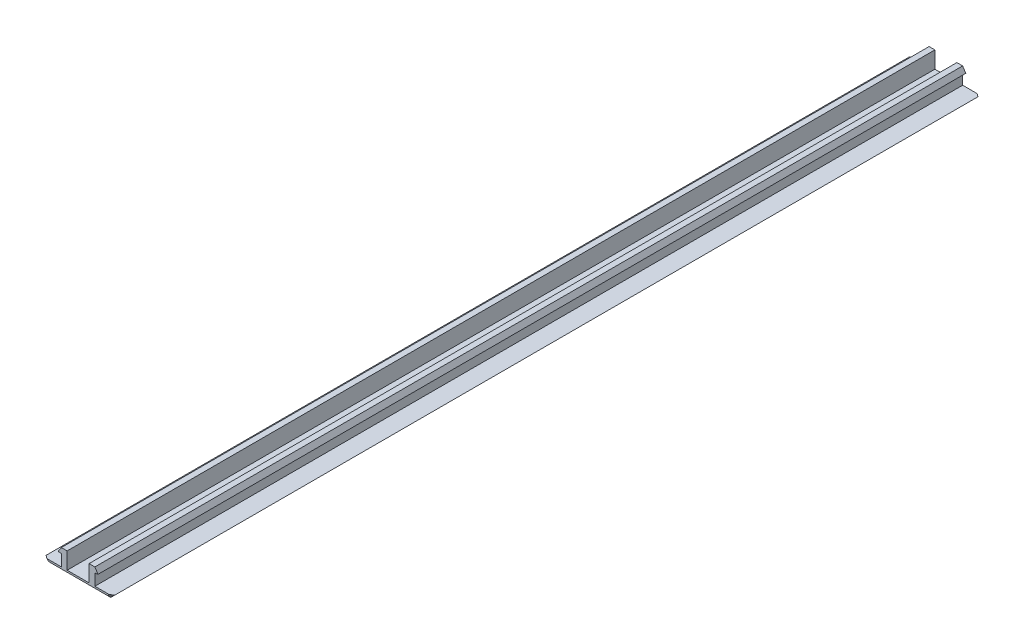
SolidWorks part; units mm, degrees
ref_plane "Front Plane" through (0, 0, 0) normal (0, 0, 1) x (1, 0, 0)
ref_plane "Top Plane" through (0, 0, 0) normal (0, 1, 0) x (1, 0, 0)
ref_plane "Right Plane" through (0, 0, 0) normal (1, 0, 0) x (0, 0, -1)
sketch "Sketch1" plane through (0, 0, 0) normal (0, 0, 1) x (1, 0, 0)
  line L0 (5.95, 0.7071) -> (2.9, 0.7071)
  line L1 (2.9, 0.7071) -> (2.9, 2.6888)
  line L2 (2.9, 2.6888) -> (3.4381, 2.7596)
  line L3 (3.4381, 2.7596) -> (2.9, 3.6007)
  line L4 (2.9, 3.6007) -> (1.9, 3.6007)
  line L5 (1.9, 3.6007) -> (1.9, 0.7071)
  line L6 (1.9, 0.7071) -> (-1.9, 0.7071)
  line L7 (0, 0.7071) -> (0, 0) construction
  line L8 (-5.2429, 0) -> (5.2429, 0)
  line L10 (6.545, 0) -> (-6.545, 0) construction
  line L11 (0, -1.9804) -> (0, 1.9804) construction
  line L15 (-1.9, 3.6007) -> (-1.9, 0.7071)
  line L16 (-5.2429, 0) -> (-5.95, 0.7071)
  line L17 (-5.95, 0.7071) -> (-2.9, 0.7071)
  line L18 (-2.9, 0.7071) -> (-2.9, 2.6888)
  line L19 (-2.9, 2.6888) -> (-3.4381, 2.7596)
  line L20 (-3.4381, 2.7596) -> (-2.9, 3.6007)
  line L21 (-2.9, 3.6007) -> (-1.9, 3.6007)
  line L22 (5.95, 0.7071) -> (5.2429, 0)
  line L23 (-5.95, 0.7071) -> (-5.2429, 0)
  point P8 (2.9, 0.7812)
  dimension "D2" = 2.8936
  dimension "D3" = 1.9
  dimension "D4" = 1
  dimension "D5" = 3.05
  dimension "D6" = 1
  dimension "D7" = 7.5
  dimension "D8" = 1.9817
  dimension "D9" = 57.39
  dimension "D10" = 45
  dimension "D11" = 45
  dimension "D12" = 0.7071
extrude "Boss-Extrude1" add sketch "Sketch1" along normal blind 150 contours L6 L7 L8 L22 L0 L1 L2 L3 L4 L5 | L7 L6 L15 L21 L20 L19 L18 L17 L16 L8
chamfer "Chamfer2" distance 0.4 angle 45 6 edges at (-5.5964, 0.3536, 150) (0, 0, 150) (5.5964, 0.3536, 150) (-5.5964, 0.3536, 0) (0, 0, 0) (5.5964, 0.3536, 0)
equation "\"Length\"= 150mm"
equation "\"D1@Boss-Extrude1\"=\"Length\""
